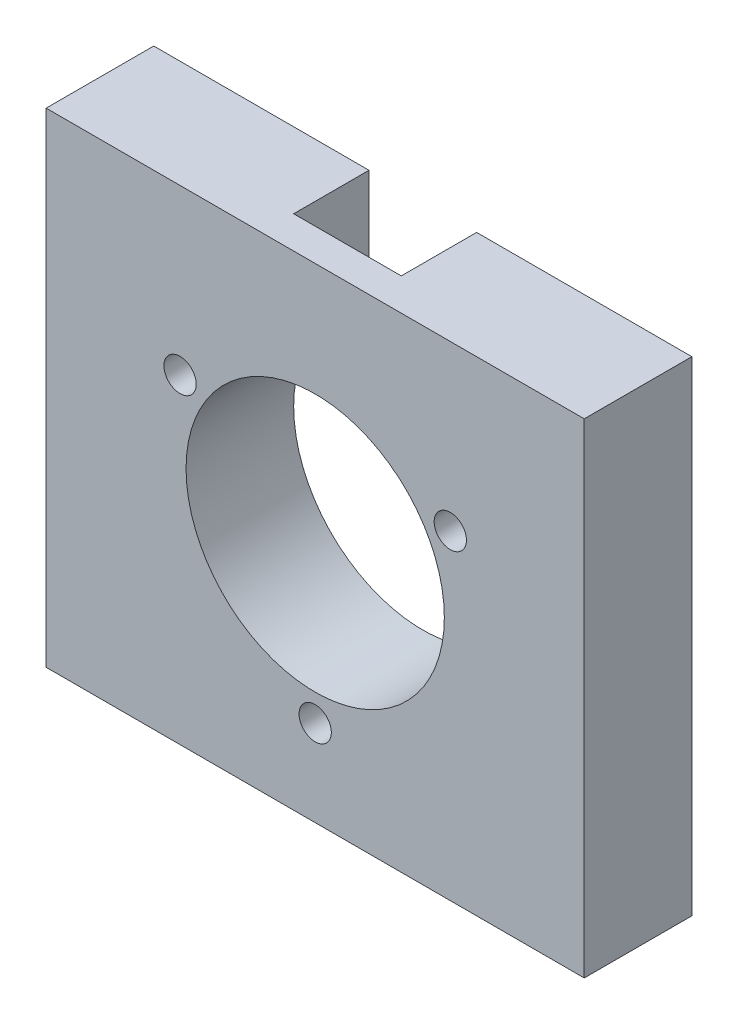
SolidWorks part; units mm, degrees
ref_plane "Plan de face" through (0, 0, 0) normal (0, 0, 1) x (1, 0, 0)
ref_plane "Plan de dessus" through (0, 0, 0) normal (0, 1, 0) x (1, 0, 0)
ref_plane "Plan de droite" through (0, 0, 0) normal (1, 0, 0) x (0, 0, -1)
sketch "Esquisse1" plane through (0, 0, 0) normal (0, 1, 0) x (1, 0, 0)
  line L0 (0, 0) -> (50, 0)
  line L1 (50, 0) -> (50, -10)
  line L2 (50, -10) -> (0, -10)
  line L3 (0, 0) -> (0, -10)
extrude "Extrusion1" add sketch "Esquisse1" along normal blind 45
sketch "Esquisse2" plane through (0, 0, 10) normal (0, 0, 1) x (1, 0, 0)
  circle A0 centre (25, 22.5) radius 12
  circle A1 centre (12.445, 29.7486) radius 1.5
  circle A2 centre (37.555, 29.7486) radius 1.5
  circle A3 centre (25, 8.0027) radius 1.5
extrude "Extrusion2" cut sketch "Esquisse2" against normal blind 45
sketch "Esquisse3" plane through (0, 0, 0) normal (0, 0, 1) x (1, 0, 0)
  line L0 (30, 33.4087) -> (30, 45)
  line L1 (20, 45) -> (30, 45)
  line L4 (20, 33.4087) -> (20, 45)
  arc A1 (30, 33.4087) -> (20, 33.4087) centre (25, 22.5) ccw
extrude "Extrusion5" cut sketch "Esquisse3" along normal blind 7
